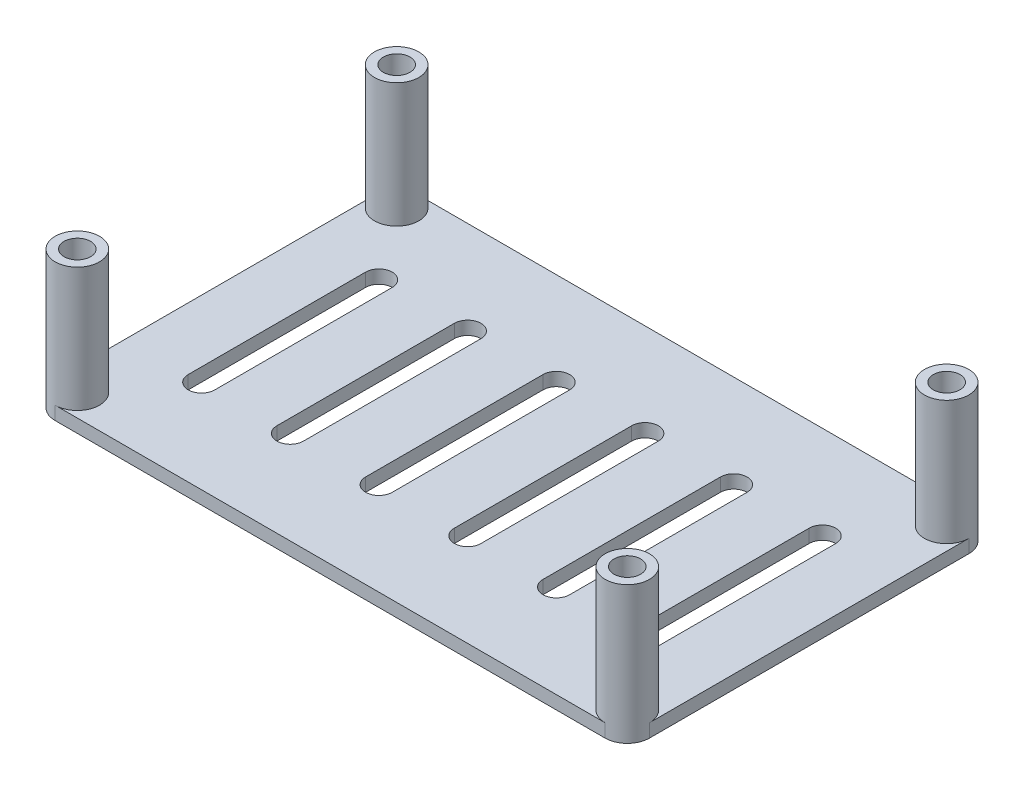
SolidWorks part; units mm, degrees
ref_plane "Front Plane" through (0, 0, 0) normal (0, 0, 1) x (1, 0, 0)
ref_plane "Top Plane" through (0, 0, 0) normal (0, 1, 0) x (1, 0, 0)
ref_plane "Right Plane" through (0, 0, 0) normal (1, 0, 0) x (0, 0, -1)
sketch "Sketch3" plane through (0, 0, 0) normal (0, 1, 0) x (1, 0, 0)
  line L0 (-31, 18) -> (31, 18) construction
  line L1 (31, 18) -> (31, -18) construction
  line L2 (31, -18) -> (-31, -18) construction
  line L3 (-31, -18) -> (-31, 18) construction
  line L4 (-31, 18) -> (31, -18) construction
  line L5 (31, 18) -> (-31, -18) construction
  circle A0 centre (-31, 18) radius 1.5
  circle A1 centre (31, 18) radius 1.5
  circle A2 centre (31, -18) radius 1.5
  circle A3 centre (-31, -18) radius 1.5
  circle A4 centre (-31, 18) radius 2.5
  circle A5 centre (31, 18) radius 2.5
  circle A6 centre (31, -18) radius 2.5
  circle A7 centre (-31, -18) radius 2.5
  dimension "D3" = 3
  dimension "D4" = 3
  dimension "D5" = 3
  dimension "D6" = 3
  dimension "D7" = 5
  dimension "D8" = 5
  dimension "D9" = 5
  dimension "D10" = 5
  dimension "D1" = 62
  dimension "D2" = 36
extrude "Boss-Extrude2" add sketch "Sketch3" along normal blind 14
sketch "Sketch4" plane through (0, 0, 0) normal (0, -1, 0) x (1, 0, 0)
  line L1 (-31, 20.5) -> (31, 20.5)
  line L2 (-33.5, 18) -> (-33.5, -18)
  line L3 (-31, -20.5) -> (31, -20.5)
  line L4 (33.5, 18) -> (33.5, -18)
  line L5 (-33.5, 20.5) -> (33.5, -20.5) construction
  line L6 (-33.5, -20.5) -> (33.5, 20.5) construction
  circle A3 centre (-31, 18) radius 2.5 construction
  arc A4 (-33.5, -18) -> (-31, -20.5) centre (-31, -18) ccw
  arc A5 (31, -20.5) -> (33.5, -18) centre (31, -18) ccw
  arc A6 (31, 20.5) -> (33.5, 18) centre (31, 18) cw
  arc A7 (-31, 20.5) -> (-33.5, 18) centre (-31, 18) ccw
  point P0 (0, 0)
  dimension "D1" = 2.5
extrude "Boss-Extrude3" add sketch "Sketch4" along normal blind 1.5
sketch "Sketch5" plane through (0, 0, 0) normal (0, 1, 0) x (1, 0, 0)
  circle A0 centre (31, 18) radius 1.5 construction
  circle A1 centre (-31, 18) radius 1.5 construction
  circle A2 centre (-31, -18) radius 1.5 construction
  circle A3 centre (31, -18) radius 1.5 construction
  circle A4 centre (31, 18) radius 1.5
  circle A5 centre (-31, 18) radius 1.5
  circle A6 centre (-31, -18) radius 1.5
  circle A7 centre (31, -18) radius 1.5
extrude "Cut-Extrude1" cut sketch "Sketch5" against normal blind 1.5
sketch "Sketch6" plane through (0, 0, 0) normal (0, 1, 0) x (1, 0, 0)
  line L0 (-25, 10) -> (-25, -10) construction
  line L1 (-23.5, 10) -> (-23.5, -10)
  line L2 (-26.5, 10) -> (-26.5, -10)
  line L3 (-15, 10) -> (-15, -10) construction
  line L4 (-13.5, 10) -> (-13.5, -10)
  line L5 (-16.5, 10) -> (-16.5, -10)
  line L6 (-5, 10) -> (-5, -10) construction
  line L7 (-3.5, 10) -> (-3.5, -10)
  line L8 (-6.5, 10) -> (-6.5, -10)
  line L9 (5, 10) -> (5, -10) construction
  line L10 (6.5, 10) -> (6.5, -10)
  line L11 (3.5, 10) -> (3.5, -10)
  line L12 (15, 10) -> (15, -10) construction
  line L13 (16.5, 10) -> (16.5, -10)
  line L14 (13.5, 10) -> (13.5, -10)
  line L15 (25, 10) -> (25, -10) construction
  line L16 (26.5, 10) -> (26.5, -10)
  line L17 (23.5, 10) -> (23.5, -10)
  arc A0 (-23.5, 10) -> (-26.5, 10) centre (-25, 10) ccw
  arc A1 (-26.5, -10) -> (-23.5, -10) centre (-25, -10) ccw
  arc A2 (-13.5, 10) -> (-16.5, 10) centre (-15, 10) ccw
  arc A3 (-16.5, -10) -> (-13.5, -10) centre (-15, -10) ccw
  arc A4 (-3.5, 10) -> (-6.5, 10) centre (-5, 10) ccw
  arc A5 (-6.5, -10) -> (-3.5, -10) centre (-5, -10) ccw
  arc A6 (6.5, 10) -> (3.5, 10) centre (5, 10) ccw
  arc A7 (3.5, -10) -> (6.5, -10) centre (5, -10) ccw
  arc A8 (16.5, 10) -> (13.5, 10) centre (15, 10) ccw
  arc A9 (13.5, -10) -> (16.5, -10) centre (15, -10) ccw
  arc A10 (26.5, 10) -> (23.5, 10) centre (25, 10) ccw
  arc A11 (23.5, -10) -> (26.5, -10) centre (25, -10) ccw
  point P2 (-25, 0)
  point P12 (-15, 0)
  point P19 (-5, 0)
  point P26 (5, 0)
  point P33 (15, 0)
  point P40 (25, 0)
  dimension "D2" = 1.5
  dimension "D3" = 20
  dimension "D1" = 25
  dimension "D4" = 6
extrude "Cut-Extrude2" cut sketch "Sketch6" against normal blind 1.5
